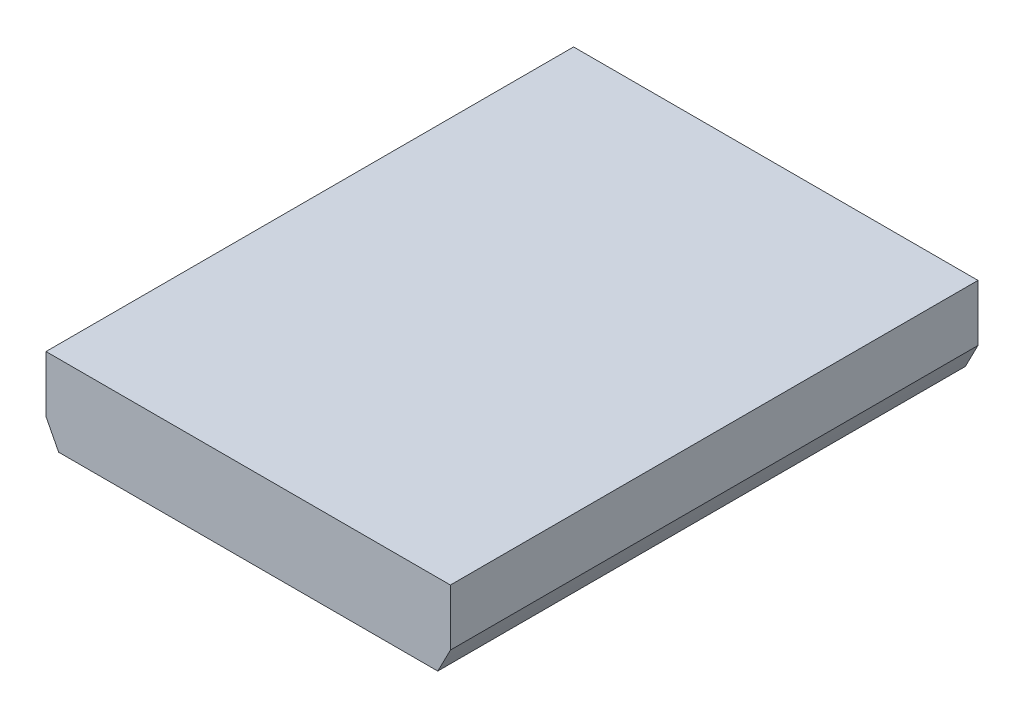
SolidWorks part; units mm, degrees
ref_plane "Front Plane" through (0, 0, 0) normal (0, 0, 1) x (1, 0, 0)
ref_plane "Top Plane" through (0, 0, 0) normal (0, 1, 0) x (1, 0, 0)
ref_plane "Right Plane" through (0, 0, 0) normal (1, 0, 0) x (0, 0, -1)
sketch "Sketch2" plane through (0, 0, 0) normal (0, 0, 1) x (1, 0, 0)
  line L0 (-127, 127) -> (127, 127)
  spline S0 degree 2 poles (-143.0272, 161.0769) (0, -161.0769) (143.0272, 161.0769) knots 0 0 0 1 1 1 construction
  spline S1 degree 2 poles (-127, 127) (0, -127) (127, 127) knots 0.056028 0.056028 0.056028 0.943972 0.943972 0.943972
extrude "Boss-Extrude2" add sketch "Sketch2" along normal blind 331.382
sketch "Sketch3" plane through (0, 127, 0) normal (0, 1, 0) x (1, 0, 0)
  line L0 (0, -309.5365) -> (0, 0) construction
  line L1 (-33, -21.8455) -> (33, -21.8455)
  line L2 (-33, -21.8455) -> (-33, -143.8455)
  line L3 (-33, -143.8455) -> (33, -143.8455)
  line L4 (33, -21.8455) -> (33, -143.8455)
  line L5 (-33, -187.5365) -> (33, -187.5365)
  line L6 (-33, -187.5365) -> (-33, -309.5365)
  line L7 (-33, -309.5365) -> (33, -309.5365)
  line L8 (33, -187.5365) -> (33, -309.5365)
  line L9 (-127, -165.691) -> (127, -165.691) construction
  line L10 (-127, -331.382) -> (-127, 0) construction
  line L11 (127, -331.382) -> (127, 0) construction
  line L12 (-33, -143.8455) -> (-33, -165.691) construction
  line L13 (33, -187.5365) -> (33, -165.691) construction
  line L14 (-33, -21.8455) -> (-33, 0) construction
  line L15 (127, 0) -> (-127, 0) construction
  dimension "D1" = 122
  dimension "D2" = 66
extrude "Cut-Extrude2" cut sketch "Sketch3" against normal through all
sketch "Sketch4" plane through (0, 0, 0) normal (0, 0, -1) x (-1, 0, 0)
  line L1 (-120, 111.6) -> (120, 111.6)
  line L2 (-120, 111.6) -> (-120, 0)
  line L3 (-120, 0) -> (120, 0)
  line L4 (120, 111.6) -> (120, 0)
  dimension "D1" = 111.6
  dimension "D2" = 240
extrude "Cut-Extrude3" cut sketch "Sketch4" against normal through all
sketch "Sketch5" plane through (0, 0, 331.382) normal (0, 0, 1) x (1, 0, 0)
  line L1 (-127, 127) -> (127, 127)
  line L2 (-127, 127) -> (-127, 162.4)
  line L3 (-127, 162.4) -> (127, 162.4)
  line L4 (127, 127) -> (127, 162.4)
  dimension "D1" = 35.4
extrude "Boss-Extrude3" add sketch "Sketch5" against normal blind 331.382
